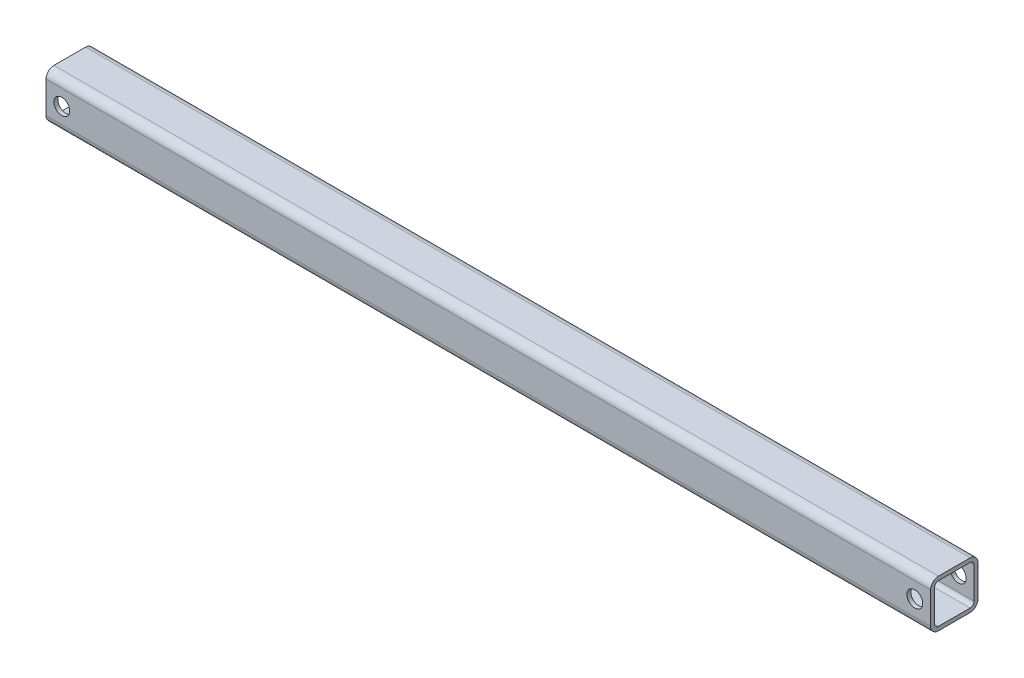
SolidWorks part; units mm, degrees
ref_plane "Front Plane" through (0, 0, 0) normal (0, 0, 1) x (1, 0, 0)
ref_plane "Top Plane" through (0, 0, 0) normal (0, 1, 0) x (1, 0, 0)
ref_plane "Right Plane" through (0, 0, 0) normal (1, 0, 0) x (0, 0, -1)
sketch3d "3DSketch1"
  line L0 (0, 0, 0) -> (711.2, 0, 0)
  dimension "D1" = 711.2
other "Structural Member1"
ref_plane "Plane1" through (0, 0, 0) normal (1, 0, 0) x (0, 0, -1)
sketch "Sketch1" plane through (0, 0, 0) normal (1, 0, 0) x (0, 0, -1)
  line L0 (-12.7, -15.875) -> (12.7, -15.875)
  line L1 (-15.875, -12.7) -> (-15.875, 12.7)
  line L2 (12.7, 15.875) -> (-12.7, 15.875)
  line L3 (15.875, 12.7) -> (15.875, -12.7)
  line L4 (-12.7, -19.05) -> (12.7, -19.05)
  line L5 (-19.05, -12.7) -> (-19.05, 12.7)
  line L6 (12.7, 19.05) -> (-12.7, 19.05)
  line L7 (19.05, 12.7) -> (19.05, -12.7)
  line L8 (-19.05, 0) -> (-15.875, 0) construction
  line L9 (-15.875, 0) -> (15.875, 0) construction
  line L10 (15.875, 0) -> (19.05, 0) construction
  line L11 (0, 19.05) -> (0, 15.875) construction
  line L12 (0, 15.875) -> (0, -15.875) construction
  line L13 (0, -15.875) -> (0, -19.05) construction
  arc A0 (19.05, 12.7) -> (12.7, 19.05) centre (12.7, 12.7) ccw
  arc A1 (12.7, -19.05) -> (19.05, -12.7) centre (12.7, -12.7) ccw
  arc A2 (-19.05, -12.7) -> (-12.7, -19.05) centre (-12.7, -12.7) ccw
  arc A3 (-12.7, 19.05) -> (-19.05, 12.7) centre (-12.7, 12.7) ccw
  arc A4 (-12.7, 15.875) -> (-15.875, 12.7) centre (-12.7, 12.7) ccw
  arc A5 (15.875, 12.7) -> (12.7, 15.875) centre (12.7, 12.7) ccw
  arc A6 (12.7, -15.875) -> (15.875, -12.7) centre (12.7, -12.7) ccw
  arc A7 (-15.875, -12.7) -> (-12.7, -15.875) centre (-12.7, -12.7) ccw
  point P6 (-19.05, -19.05)
  point P33 (-19.05, 19.05)
  point P35 (19.05, 19.05)
  point P36 (19.05, -19.05)
  point P37 (0, 0)
  dimension "D1" = 6.35
  dimension "Thickness" = 3.175
  dimension "V_leg" = 38.1
  dimension "H_leg" = 38.1
sketch "Sketch2" plane through (0, 0, 19.05) normal (0, 0, 1) x (1, 0, 0)
  line L0 (0, 0) -> (711.2, 0) construction
  line L1 (711.2, 12.7) -> (711.2, -12.7) construction
  line L2 (0, 12.7) -> (0, -12.7) construction
  circle A0 centre (12.7, 0) radius 6.35
  dimension "D1" = 12.7
  dimension "D2" = 12.7
extrude "Cut-Extrude1" cut sketch "Sketch2" against normal through all
sketch "Sketch3" plane through (0, 0, 19.05) normal (0, 0, 1) x (1, 0, 0)
  line L0 (711.2, 12.7) -> (711.2, -12.7) construction
  circle A0 centre (698.5, 0) radius 6.35
  dimension "D1" = 12.7
  dimension "D2" = 12.7
extrude "Cut-Extrude2" cut sketch "Sketch3" against normal through all
